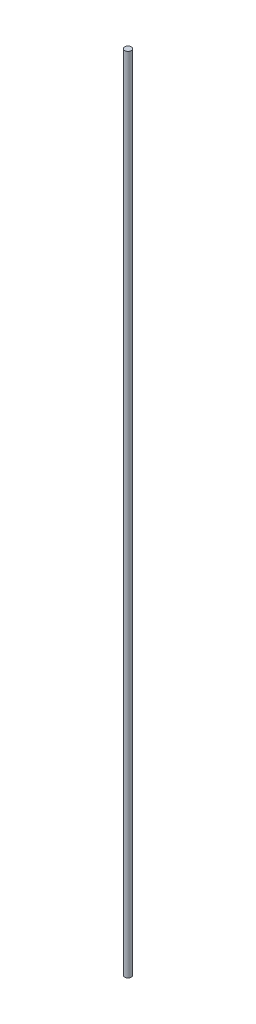
SolidWorks part; units mm, degrees
ref_plane "Front Plane" through (0, 0, 0) normal (0, 0, 1) x (1, 0, 0)
ref_plane "Top Plane" through (0, 0, 0) normal (0, 1, 0) x (1, 0, 0)
ref_plane "Right Plane" through (0, 0, 0) normal (1, 0, 0) x (0, 0, -1)
sketch "Sketch1" plane through (0, 0, 0) normal (0, 1, 0) x (1, 0, 0)
  circle A0 centre (0, 0) radius 4
  dimension "D1" = 8
extrude "Boss-Extrude1" add sketch "Sketch1" along normal blind 974
